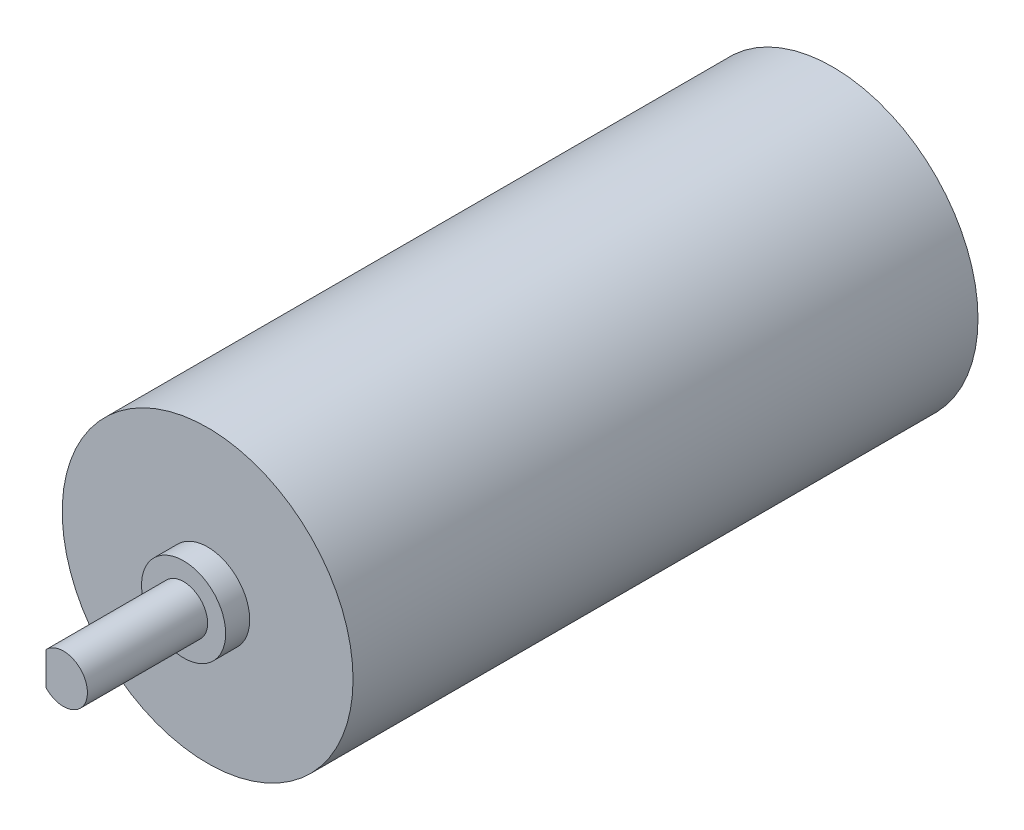
SolidWorks part; units mm, degrees
ref_plane "Front Plane" through (0, 0, 0) normal (0, 0, 1) x (1, 0, 0)
ref_plane "Top Plane" through (0, 0, 0) normal (0, 1, 0) x (1, 0, 0)
ref_plane "Right Plane" through (0, 0, 0) normal (1, 0, 0) x (0, 0, -1)
sketch "Sketch1" plane through (0, 0, 0) normal (0, 0, 1) x (1, 0, 0)
  circle A0 centre (0, 0) radius 12.1
  dimension "D1" = 24.2
extrude "Boss-Extrude1" add sketch "Sketch1" along normal blind 52
sketch "Sketch2" plane through (0, 0, 52) normal (0, 0, 1) x (1, 0, 0)
  circle A0 centre (0, 0) radius 3.5
  dimension "D1" = 7
extrude "Boss-Extrude2" add sketch "Sketch2" along normal blind 2
sketch "Sketch4" plane through (0, 0, 54) normal (0, 0, 1) x (1, 0, 0)
  line L0 (-1.4493, 1.3782) -> (-1.4493, -1.3782)
  arc A0 (-1.4493, -1.3782) -> (-1.4493, 1.3782) centre (0, 0) ccw
  dimension "D1" = 4
extrude "Boss-Extrude3" add sketch "Sketch4" along normal blind 10
